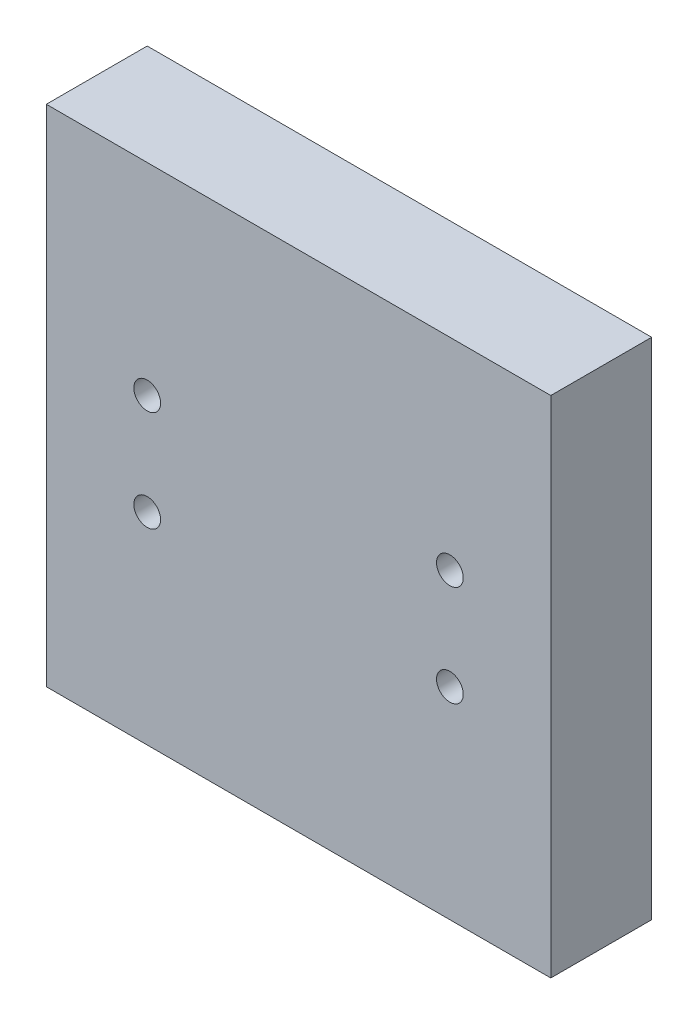
SolidWorks part; units mm, degrees
ref_plane "Front Plane" through (0, 0, 0) normal (0, 0, 1) x (1, 0, 0)
ref_plane "Top Plane" through (0, 0, 0) normal (0, 1, 0) x (1, 0, 0)
ref_plane "Right Plane" through (0, 0, 0) normal (1, 0, 0) x (0, 0, -1)
sketch "Sketch1" plane through (0, 0, 0) normal (0, 0, 1) x (1, 0, 0)
  line L1 (-50, -50) -> (50, -50)
  line L2 (-50, -50) -> (-50, 50)
  line L3 (-50, 50) -> (50, 50)
  line L4 (50, -50) -> (50, 50)
  line L5 (-50, -50) -> (50, 50) construction
  line L6 (-50, 50) -> (50, -50) construction
  line L7 (-30, -10) -> (30, -10) construction
  line L8 (-30, -10) -> (-30, 10) construction
  line L9 (-30, 10) -> (30, 10) construction
  line L10 (30, -10) -> (30, 10) construction
  line L11 (-30, -10) -> (30, 10) construction
  line L12 (-30, 10) -> (30, -10) construction
  point P0 (0, 0)
  point P6 (0, 0)
extrude "Boss-Extrude1" add sketch "Sketch1" along normal blind 20
hole_wizard "CSK for M5 Flat Head Machine Screw1" positions "Sketch3" profile "Sketch2" countersink size "M5" standard "Ansi Metric" end condition through all
sketch "Sketch3" plane through (0, 0, 0) normal (0, 0, -1) x (-1, 0, 0)
  point P1 (-30, 10)
  point P4 (30, 10)
  point P7 (30, -10)
  point P10 (-30, -10)
sketch "Sketch2" plane through (30, 10, 0) normal (1, 0, 0) x (0, 1, 0)
  line L0 (0, 0) -> (0, 20)
  line L1 (0, 20) -> (2.65, 20)
  line L2 (2.65, 20) -> (2.65, 2.55)
  line L3 (2.65, 2.55) -> (5.2, 0)
  line L5 (5.2, 0) -> (0, 0)
  line L6 (-2.65, 2.55) -> (-5.2, 0) construction
  line L11 (0, -6.35) -> (0, 107.95) construction
  dimension "Thru Hole Dia." = 5.3
  dimension "Thru Hole Depth" = 20
  dimension "Near C'Sink Dia." = 10.4
  dimension "Near C'Sink Angle" = 90
sketch "Sketch4" plane through (0, 0, 20) normal (0, 0, 1) x (1, 0, 0)
  circle A0 centre (-3, -0.35) radius 1.25
